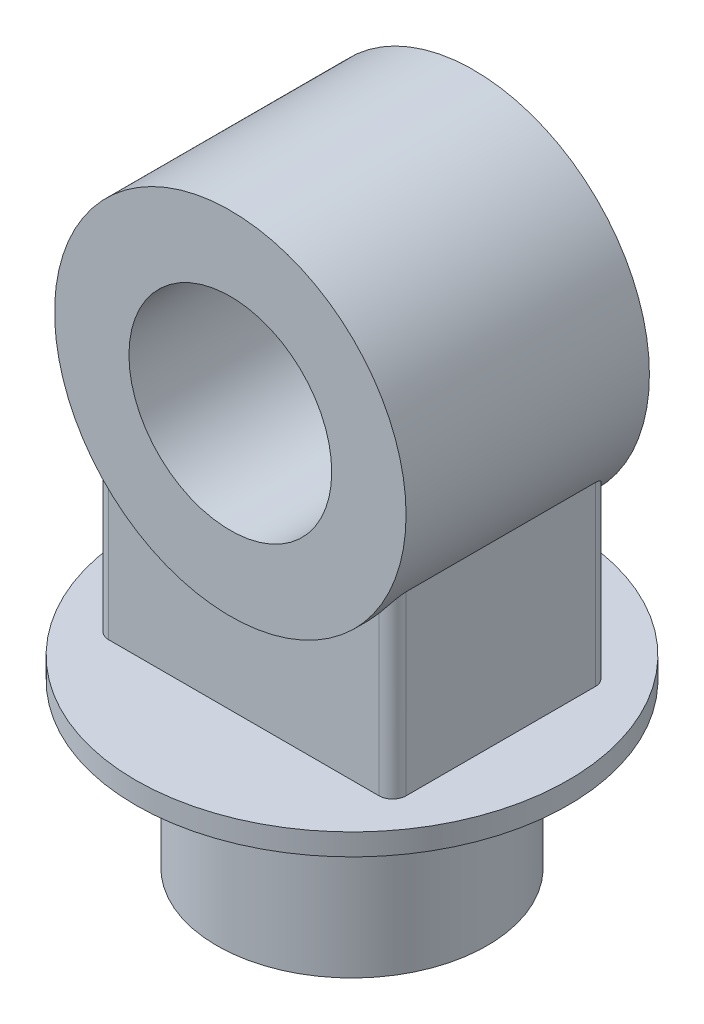
SolidWorks part; units mm, degrees
ref_plane "Front Plane" through (0, 0, 0) normal (0, 0, 1) x (1, 0, 0)
ref_plane "Top Plane" through (0, 0, 0) normal (0, 1, 0) x (1, 0, 0)
ref_plane "Right Plane" through (0, 0, 0) normal (1, 0, 0) x (0, 0, -1)
sketch "Sketch1" plane through (0, 0, 0) normal (0, 1, 0) x (1, 0, 0)
  circle A0 centre (0, 0) radius 100
  dimension "D1" = 200
extrude "Boss-Extrude1" add sketch "Sketch1" along normal blind 120
sketch "Sketch2" plane through (0, 120, 0) normal (0, 1, 0) x (1, 0, 0)
  circle A0 centre (0, 0) radius 160
  dimension "D1" = 320
extrude "Boss-Extrude2" add sketch "Sketch2" along normal blind 16
sketch "Sketch3" plane through (0, 0, 0) normal (0, 0, 1) x (1, 0, 0)
  line L0 (160, 136) -> (-160, 136) construction
  circle A0 centre (0, 336) radius 75
  circle A1 centre (0, 336) radius 130
  point P3 (0, 0)
  dimension "D1" = 150
  dimension "D2" = 260
  dimension "D3" = 200
extrude "Boss-Extrude3" add sketch "Sketch3" along normal mid plane 180 separate body
sketch "Sketch4" plane through (0, 136, 0) normal (0, 1, 0) x (1, 0, 0)
  line L1 (-110, -80) -> (110, -80)
  line L2 (-110, -80) -> (-110, 80)
  line L3 (-110, 80) -> (110, 80)
  line L4 (110, -80) -> (110, 80)
  line L5 (-110, -80) -> (110, 80) construction
  line L6 (-110, 80) -> (110, -80) construction
  point P0 (0, 0)
  dimension "D1" = 160
  dimension "D2" = 220
extrude "Boss-Extrude4" add sketch "Sketch4" along normal up to next
fillet "Fillet1" radius 10 4 edges at (-110, 201.359, 80) (110, 201.359, 80) (-110, 201.359, -80) (110, 201.359, -80)
